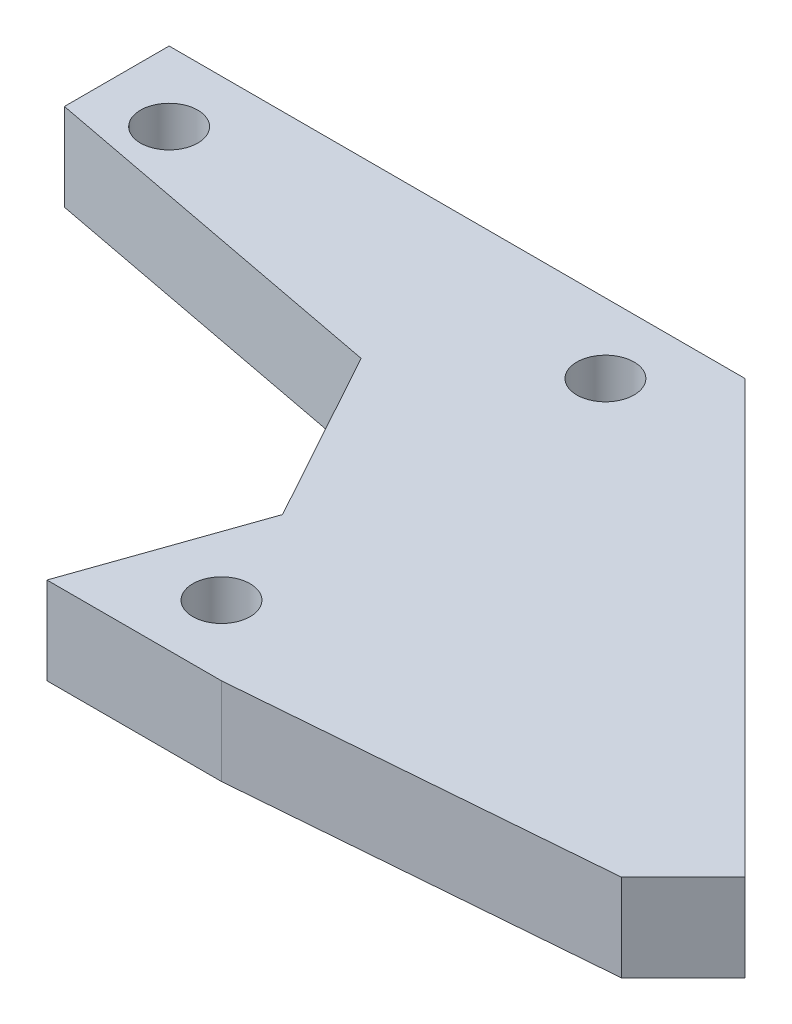
SolidWorks part; units mm, degrees
ref_plane "Front Plane" through (0, 0, 0) normal (0, 0, 1) x (1, 0, 0)
ref_plane "Top Plane" through (0, 0, 0) normal (0, 1, 0) x (1, 0, 0)
ref_plane "Right Plane" through (0, 0, 0) normal (1, 0, 0) x (0, 0, -1)
other "Bounding Box"
ref_plane "Default Plane" through (13.8565, 3.175, 6.7999) normal (0, -1, 0) x (-1, 0, 0)
sketch "Sketch2" plane through (0, 0, 0) normal (0, 1, 0) x (1, 0, 0)
  line L1 (63.5, 19.05) -> (94.9309, -12.3809)
  line L3 (26.67, 13.97) -> (58.42, 13.97) construction
  line L4 (58.42, 13.97) -> (58.42, -13.97) construction
  line L5 (58.42, -13.97) -> (58.42, -19.05) construction
  line L7 (90.4408, -16.871) -> (94.9309, -12.3809)
  line L8 (58.42, 13.97) -> (58.42, 19.05) construction
  line L9 (63.5, 19.05) -> (-63.5, 19.05) construction
  line L10 (63.5, 19.05) -> (63.5, -19.05) construction
  line L11 (63.5, -19.05) -> (-63.5, -19.05) construction
  line L12 (-63.5, 19.05) -> (-63.5, -19.05) construction
  line L13 (63.5, 19.05) -> (-63.5, -19.05) construction
  line L14 (63.5, -19.05) -> (-63.5, 19.05) construction
  line L15 (26.67, 13.97) -> (26.67, 19.05) construction
  line L16 (58.42, -13.97) -> (63.5, -13.97) construction
  line L19 (48.26, 6.35) -> (21.59, 11.43)
  line L20 (21.59, 11.43) -> (21.59, 19.05)
  line L21 (21.59, 19.05) -> (63.5, 19.05)
  line L22 (90.4408, -16.871) -> (63.5, -19.05)
  line L23 (63.5, -19.05) -> (50.8, -19.05)
  line L24 (26.67, 13.97) -> (21.59, 13.97) construction
  line L25 (48.26, 6.35) -> (58.42, 13.97) construction
  line L26 (48.26, 6.35) -> (55.245, -6.35)
  line L27 (55.245, -6.35) -> (50.8, -19.05)
  circle A0 centre (58.42, 13.97) radius 2.0828
  circle A1 centre (26.67, 13.97) radius 2.0828
  circle A2 centre (58.42, -13.97) radius 2.0828
  point P2 (21.1085, 10.9485)
  point P13 (58.42, 0)
  point P16 (0, 0)
  point P20 (63.5, 0)
  point P25 (52.3875, 1.27)
  point P27 (58.42, 12.4458)
  point P29 (53.8873, 1.27)
  point P30 (54.3462, 1.27)
  point P31 (54.6572, 1.8402)
  point P32 (51.8991, 3.3098)
  point P33 (47.4386, -19.05)
  point P34 (55.1969, -5.3071)
  point P35 (55.1434, -5.7887)
  point P36 (0, 0)
  point P37 (55.1434, -5.7887)
  point P38 (48.26, 6.35)
  point P39 (50.8, -19.05)
  point P40 (55.285, -6.35)
  dimension "D2" = 4.1656
  dimension "D3" = 45
  dimension "D4" = 5.08
  dimension "D5" = 31.75
  dimension "D6" = 12.7
  dimension "D7" = 44.45
  dimension "D8" = 38.1
  dimension "D9" = 6.35
  dimension "D10" = 127
  dimension ".2" = 5.08
  dimension "D11" = 2.54
  dimension "D12" = 12.7
  dimension "D13" = 12.7
  dimension "D14" = 12.7
  dimension "D15" = 3.175
extrude "Boss-Extrude1" add sketch "Sketch2" along normal blind 6.35
